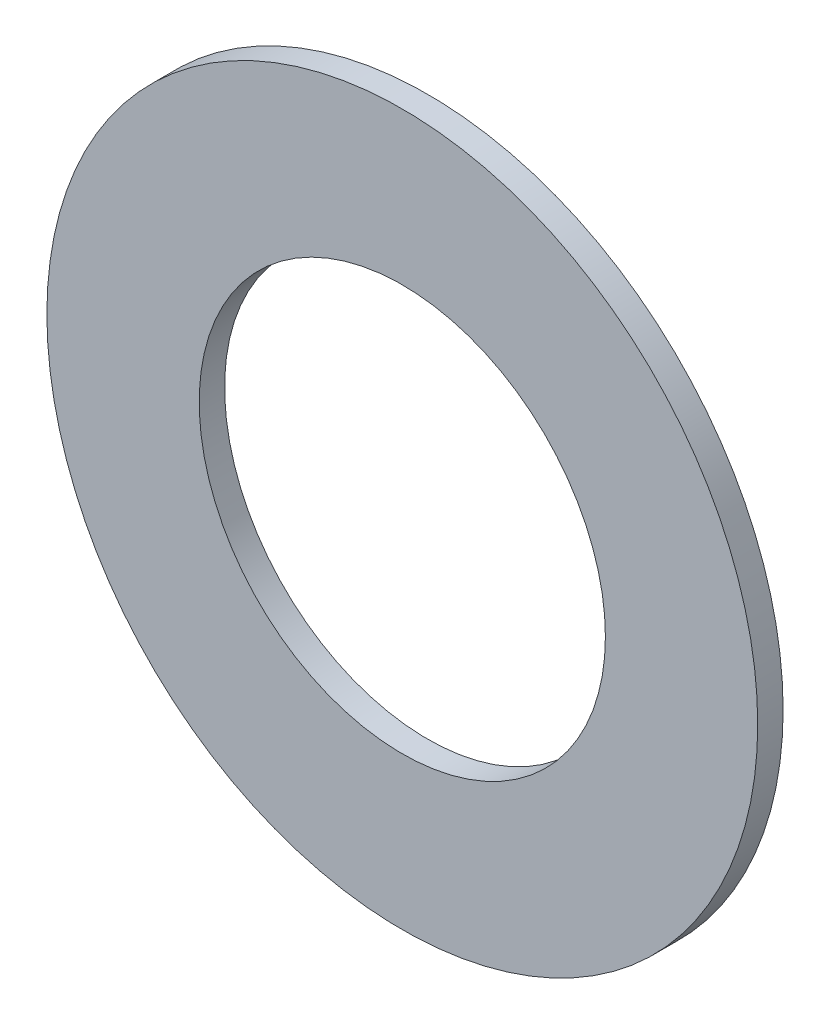
SolidWorks part; units mm, degrees
material "Stainless Steel (ferritic)"
ref_plane "Front Plane" through (0, 0, 0) normal (0, 0, 1) x (1, 0, 0)
ref_plane "Top Plane" through (0, 0, 0) normal (0, 1, 0) x (1, 0, 0)
ref_plane "Right Plane" through (0, 0, 0) normal (1, 0, 0) x (0, 0, -1)
sketch "Sketch1" plane through (0, 0, 0) normal (0, 0, 1) x (1, 0, 0)
  circle A0 centre (0, 0) radius 4
  circle A1 centre (0, 0) radius 7
  dimension "D1" = 8
  dimension "D2" = 14
extrude "Boss-Extrude1" add sketch "Sketch1" along normal blind 0.5
